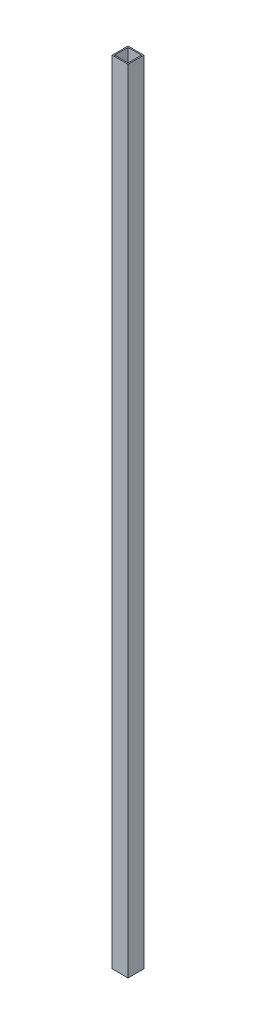
SolidWorks part; units mm, degrees
ref_plane "Front Plane" through (0, 0, 0) normal (0, 0, 1) x (1, 0, 0)
ref_plane "Top Plane" through (0, 0, 0) normal (0, 1, 0) x (1, 0, 0)
ref_plane "Right Plane" through (0, 0, 0) normal (1, 0, 0) x (0, 0, -1)
sketch "Sketch1" plane through (0, 0, 0) normal (0, 1, 0) x (1, 0, 0)
  line L0 (1.45, 18.55) -> (18.55, 18.55)
  line L1 (0, 0) -> (20, 0)
  line L2 (0, 0) -> (0, 20)
  line L3 (0, 20) -> (20, 20)
  line L4 (20, 0) -> (20, 20)
  line L5 (18.55, 1.45) -> (18.55, 18.55)
  line L6 (1.45, 1.45) -> (18.55, 1.45)
  line L7 (1.45, 1.45) -> (1.45, 18.55)
  dimension "D1" = 20
  dimension "D2" = 1.45
extrude "Boss-Extrude1" add sketch "Sketch1" along normal blind 1000
